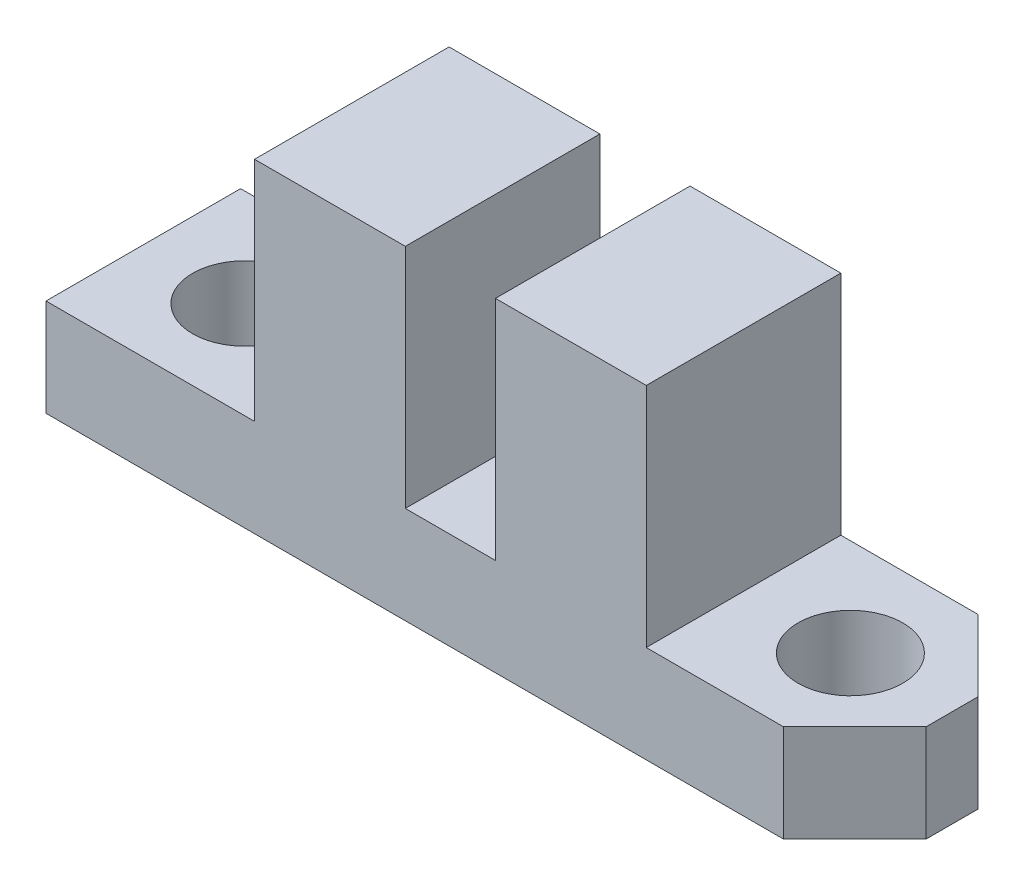
SolidWorks part; units mm, degrees
ref_plane "Front Plane" through (0, 0, 0) normal (0, 0, 1) x (1, 0, 0)
ref_plane "Top Plane" through (0, 0, 0) normal (0, 1, 0) x (1, 0, 0)
ref_plane "Right Plane" through (0, 0, 0) normal (1, 0, 0) x (0, 0, -1)
sketch "Sketch1" plane through (0, 0, 0) normal (0, 1, 0) x (1, 0, 0)
  line L1 (-12.47, -3) -> (12.47, -3)
  line L2 (-12.47, -3) -> (-12.47, 3)
  line L3 (-12.47, 3) -> (12.47, 3)
  line L4 (12.47, -3) -> (12.47, 3)
  line L5 (0, 3) -> (0, -3) construction
  line L6 (-12.47, 0) -> (12.47, 0) construction
  point P0 (0, 0)
  dimension "D1" = 24.94
  dimension "D2" = 6
extrude "Boss-Extrude1" add sketch "Sketch1" along normal blind 3
sketch "Sketch2" plane through (0, 3, 0) normal (0, 1, 0) x (1, 0, 0)
  line L0 (12.47, 3) -> (-12.47, 3) construction
  line L1 (-6.04, 3) -> (-1.39, 3)
  line L2 (-6.04, 3) -> (-6.04, -3)
  line L3 (-6.04, -3) -> (-1.39, -3)
  line L4 (-1.39, 3) -> (-1.39, -3)
  line L5 (-12.47, -3) -> (12.47, -3) construction
  line L6 (-12.47, 3) -> (-12.47, -3) construction
  dimension "D1" = 4.65
  dimension "D2" = 6.43
extrude "Boss-Extrude2" add sketch "Sketch2" along normal blind 7
sketch "Sketch3" plane through (0, 3, 0) normal (0, 1, 0) x (1, 0, 0)
  line L0 (-12.47, 3) -> (-12.47, -3) construction
  circle A0 centre (-9.335, 0) radius 1.615
  dimension "D1" = 3.23
  dimension "D2" = 3.135
extrude "Cut-Extrude1" cut sketch "Sketch3" against normal through all
mirror "Mirror1" about plane through (0, 0, 0) normal (1, 0, 0) of "Cut-Extrude1", "Boss-Extrude2"
chamfer "Chamfer2" distance 2.2 angle 45 2 edges at (12.47, 1.5, -3) (12.47, 1.5, 3)
